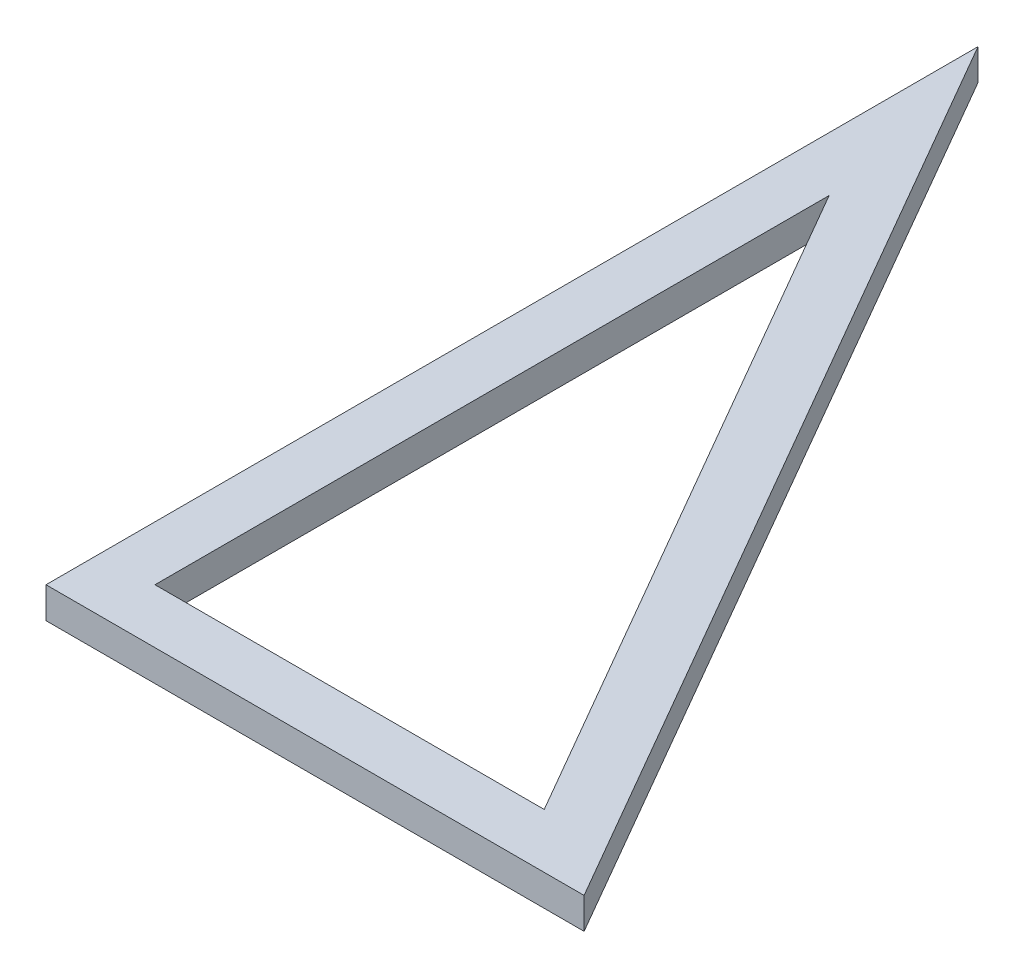
SolidWorks part; units mm, degrees
ref_plane "前视基准面" through (0, 0, 0) normal (0, 0, 1) x (1, 0, 0)
ref_plane "上视基准面" through (0, 0, 0) normal (0, 1, 0) x (1, 0, 0)
ref_plane "右视基准面" through (0, 0, 0) normal (1, 0, 0) x (0, 0, -1)
sketch "草图1" plane through (0, 0, 0) normal (0, 1, 0) x (1, 0, 0)
  line L0 (0, 86.6025) -> (0, 0)
  line L1 (0, 0) -> (50, 0)
  line L2 (50, 0) -> (0, 86.6025)
  line L3 (62.1244, -7) -> (-7, 112.7269)
  line L4 (-7, 112.7269) -> (-7, -7)
  line L5 (-7, -7) -> (62.1244, -7)
  point P3 (0, 0)
  point P4 (67.2714, 25.5678)
  point P5 (72.8377, 32.3711)
  point P6 (0, 0)
  dimension "D1" = 50
  dimension "D2" = 100
  dimension "D3" = 30
  dimension "D4" = 7
extrude "凸台-拉伸1" add sketch "草图1" along normal blind 4
